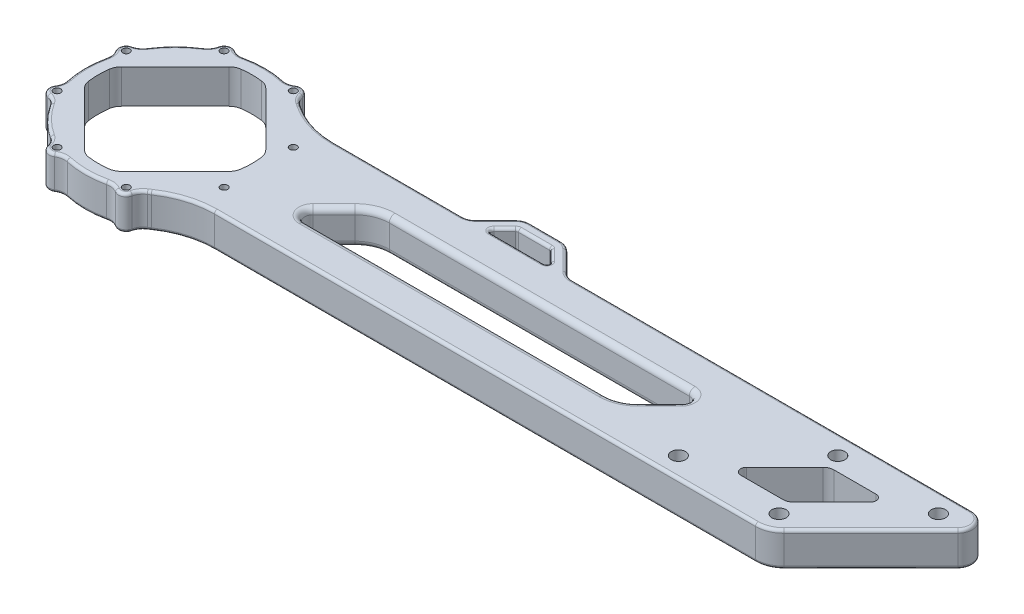
SolidWorks part; units mm, degrees
ref_plane "前视基准面" through (0, 0, 0) normal (0, 0, 1) x (1, 0, 0)
ref_plane "上视基准面" through (0, 0, 0) normal (0, 1, 0) x (1, 0, 0)
ref_plane "右视基准面" through (0, 0, 0) normal (1, 0, 0) x (0, 0, -1)
sketch "草图1" plane through (0, 0, 0) normal (0, 1, 0) x (1, 0, 0)
  line L0 (0, -31.8198) -> (31.8198, 0) construction
  line L9 (-29.3332, 12.1502) -> (-29.3332, -12.1502) construction
  line L10 (-29.3332, -12.1502) -> (-12.1502, -29.3332) construction
  line L11 (-12.1502, -29.3332) -> (12.1502, -29.3332) construction
  line L12 (12.1502, -29.3332) -> (29.3332, -12.1502) construction
  line L13 (29.3332, -12.1502) -> (29.3332, 12.1502) construction
  line L14 (29.3332, 12.1502) -> (12.1502, 29.3332) construction
  line L15 (12.1502, 29.3332) -> (-12.1502, 29.3332) construction
  line L16 (-12.1502, 29.3332) -> (-29.3332, 12.1502) construction
  line L17 (0, -31.8198) -> (-31.8198, 0) construction
  line L18 (31.8198, 0) -> (0, 31.8198) construction
  line L19 (-31.8198, 0) -> (0, 31.8198) construction
  line L20 (0, -31.8198) -> (0, 31.8198) construction
  line L21 (31.8198, 0) -> (-31.8198, 0) construction
  line L22 (-6.4825, -25.3373) -> (-25.3373, -6.4825)
  line L23 (-25.3373, 6.4825) -> (-6.4825, 25.3373)
  line L24 (6.4825, 25.3373) -> (25.3373, 6.4825)
  line L25 (25.3373, -6.4825) -> (6.4825, -25.3373)
  circle A0 centre (0, 0) radius 27 construction
  circle A1 centre (0, 0) radius 29.3332 construction
  arc A2 (-3.6168, -26.7567) -> (3.6168, -26.7567) centre (0, 0) ccw
  arc A3 (26.7567, -3.6168) -> (26.7567, 3.6168) centre (0, 0) ccw
  arc A4 (3.6168, 26.7567) -> (-3.6168, 26.7567) centre (0, 0) ccw
  arc A5 (-26.7567, -3.6168) -> (-26.7567, 3.6168) centre (0, 0) cw
  arc A6 (-3.6168, -26.7567) -> (-6.4825, -25.3373) centre (-2.947, -21.8017) cw
  arc A7 (3.6168, -26.7567) -> (6.4825, -25.3373) centre (2.947, -21.8017) ccw
  arc A8 (26.7567, -3.6168) -> (25.3373, -6.4825) centre (21.8017, -2.947) cw
  arc A9 (26.7567, 3.6168) -> (25.3373, 6.4825) centre (21.8017, 2.947) ccw
  arc A10 (3.6168, 26.7567) -> (6.4825, 25.3373) centre (2.947, 21.8017) cw
  arc A11 (-3.6168, 26.7567) -> (-6.4825, 25.3373) centre (-2.947, 21.8017) ccw
  arc A12 (-26.7567, 3.6168) -> (-25.3373, 6.4825) centre (-21.8017, 2.947) cw
  arc A13 (-26.7567, -3.6168) -> (-25.3373, -6.4825) centre (-21.8017, -2.947) ccw
  circle A14 centre (0, 0) radius 29 construction
  circle A15 centre (-12.1502, -29.3332) radius 2.75 construction
  circle A16 centre (0, 0) radius 31.75 construction
  circle A17 centre (-29.3332, -12.1502) radius 2.75 construction
  circle A18 centre (12.1502, -29.3332) radius 2.75 construction
  arc A19 (-14.8348, -29.9295) -> (-10.6736, -31.6531) centre (-12.1502, -29.3332) ccw
  arc A20 (10.6736, -31.6531) -> (14.6429, -28.1718) centre (12.1502, -29.3332) ccw construction
  arc A21 (-29.9295, -14.8348) -> (-30.2745, -9.5663) centre (-29.3332, -12.1502) cw construction
  arc A22 (-26.7942, -17.0334) -> (-17.0334, -26.7942) centre (0, 0) ccw
  arc A23 (-6.9019, -30.9907) -> (6.9019, -30.9907) centre (0, 0) ccw construction
  arc A24 (10.6736, -31.6531) -> (6.9019, -30.9907) centre (7.9888, -35.8712) ccw construction
  arc A25 (-10.6736, -31.6531) -> (-6.9019, -30.9907) centre (-7.9888, -35.8712) cw construction
  arc A26 (-14.8348, -29.9295) -> (-17.0334, -26.7942) centre (-19.7158, -31.0137) ccw
  arc A27 (-29.9295, -14.8348) -> (-26.7942, -17.0334) centre (-31.0137, -19.7158) cw
  circle A28 centre (-12.1502, -29.3332) radius 1.25
  circle A29 centre (-29.3332, -12.1502) radius 1.25
  arc A30 (-31.6531, -10.6736) -> (-29.9295, -14.8348) centre (-29.3332, -12.1502) ccw
  arc A31 (-31.6531, -10.6736) -> (-30.9907, -6.9019) centre (-35.8712, -7.9888) ccw
  arc A32 (-30.9907, 6.9019) -> (-30.9907, -6.9019) centre (0, 0) ccw
  arc A33 (-31.6531, 10.6736) -> (-30.9907, 6.9019) centre (-35.8712, 7.9888) cw
  circle A34 centre (-29.3332, 12.1502) radius 1.25
  arc A35 (-29.9295, 14.8348) -> (-31.6531, 10.6736) centre (-29.3332, 12.1502) ccw
  arc A36 (-29.9295, 14.8348) -> (-26.7942, 17.0334) centre (-31.0137, 19.7158) ccw
  arc A37 (-17.0334, 26.7942) -> (-26.7942, 17.0334) centre (0, 0) ccw
  arc A38 (-14.8348, 29.9295) -> (-17.0334, 26.7942) centre (-19.7158, 31.0137) cw
  circle A39 centre (-12.1502, 29.3332) radius 1.25
  arc A40 (-10.6736, 31.6531) -> (-14.8348, 29.9295) centre (-12.1502, 29.3332) ccw
  arc A41 (-10.6736, 31.6531) -> (-6.9019, 30.9907) centre (-7.9888, 35.8712) ccw
  arc A42 (6.9019, 30.9907) -> (-6.9019, 30.9907) centre (0, 0) ccw
  arc A43 (10.6736, 31.6531) -> (6.9019, 30.9907) centre (7.9888, 35.8712) cw
  circle A44 centre (12.1502, 29.3332) radius 1.25
  arc A45 (14.8348, 29.9295) -> (10.6736, 31.6531) centre (12.1502, 29.3332) ccw
  arc A46 (14.8348, 29.9295) -> (17.0334, 26.7942) centre (19.7158, 31.0137) ccw
  arc A47 (26.7942, 17.0334) -> (17.0334, 26.7942) centre (0, 0) ccw
  arc A48 (29.9295, 14.8348) -> (26.7942, 17.0334) centre (31.0137, 19.7158) cw
  circle A49 centre (29.3332, 12.1502) radius 1.25
  arc A50 (31.6531, 10.6736) -> (29.9295, 14.8348) centre (29.3332, 12.1502) ccw
  arc A51 (31.6531, 10.6736) -> (30.9907, 6.9019) centre (35.8712, 7.9888) ccw
  arc A52 (30.9907, -6.9019) -> (30.9907, 6.9019) centre (0, 0) ccw
  arc A53 (31.6531, -10.6736) -> (30.9907, -6.9019) centre (35.8712, -7.9888) cw
  circle A54 centre (29.3332, -12.1502) radius 1.25
  arc A55 (29.9295, -14.8348) -> (31.6531, -10.6736) centre (29.3332, -12.1502) ccw
  arc A56 (29.9295, -14.8348) -> (26.7942, -17.0334) centre (31.0137, -19.7158) ccw
  arc A57 (17.0334, -26.7942) -> (26.7942, -17.0334) centre (0, 0) ccw
  arc A58 (14.8348, -29.9295) -> (17.0334, -26.7942) centre (19.7158, -31.0137) cw
  circle A59 centre (12.1502, -29.3332) radius 1.25
  arc A60 (10.6736, -31.6531) -> (14.8348, -29.9295) centre (12.1502, -29.3332) ccw
  arc A61 (10.6736, -31.6531) -> (6.9019, -30.9907) centre (7.9888, -35.8712) ccw
  arc A62 (-6.9019, -30.9907) -> (6.9019, -30.9907) centre (0, 0) ccw
  arc A63 (-10.6736, -31.6531) -> (-6.9019, -30.9907) centre (-7.9888, -35.8712) cw
  point P13 (0, 0)
  point P32 (-5.3565, -26.4633)
  point P35 (5.3565, -26.4633)
  point P38 (26.4633, -5.3565)
  point P41 (26.4633, 5.3565)
  point P44 (5.3565, 26.4633)
  point P47 (-5.3565, 26.4633)
  point P50 (-26.4633, 5.3565)
  point P53 (-26.4633, -5.3565)
  point P72 (9.5663, -30.2745)
  point P75 (-9.5663, -30.2745)
  point P78 (-14.6429, -28.1718)
  point P81 (-28.1718, -14.6429)
  point P84 (-55.2795, -36.2672)
  point P155 (0, 0)
  dimension "D1" = 54
  dimension "D3" = 5
  dimension "D4" = 58
  dimension "D5" = 5.5
  dimension "D6" = 5
  dimension "D7" = 2.5
  dimension "D2" = 45
  dimension "D8" = 8
extrude "凸台-拉伸1" add sketch "草图1" along normal blind 12
sketch "草图2" plane through (0, 0, 0) normal (0, -1, 0) x (1, 0, 0)
  line L0 (0, 0) -> (250, 0) construction
  line L1 (23.8131, 21) -> (224.8579, 21)
  line L2 (23.8131, -21) -> (229, -21)
  line L3 (231.9289, 18.0711) -> (262.4645, -12.4645)
  line L4 (229, -21) -> (258.9289, -21)
  arc A0 (26.7942, 17.0334) -> (17.0334, 26.7942) centre (0, 0) ccw construction
  arc A1 (23.8131, 21) -> (23.8131, -21) centre (-10.231, 0) cw
  arc A2 (262.4645, -12.4645) -> (258.9289, -21) centre (258.9289, -16) cw
  arc A3 (224.8579, 21) -> (231.9289, 18.0711) centre (224.8579, 11) cw
  circle A4 centre (29.3332, 12.1502) radius 1.25
  circle A5 centre (29.3332, -12.1502) radius 1.25
  point P17 (229, 21)
  dimension "D4" = 5
  dimension "D5" = 10
  dimension "D6" = 40
  dimension "D1" = 250
  dimension "D2" = 42
  dimension "D3" = 45
extrude "凸台-拉伸2" add sketch "草图2" against normal up to surface (12 mm away) up to face at (0, 12, 0)
fillet "圆角1" radius 30 2 edges at (23.8131, 6, -21) (23.8131, 6, 21)
sketch "草图3" plane through (0, 0, 0) normal (0, -1, 0) x (1, 0, 0)
  line L0 (104.6336, -30.85) -> (93.7757, -30.85)
  line L1 (90.2402, -29.3855) -> (83.3191, -22.4645)
  line L2 (34.8147, -21) -> (258.9289, -21) construction
  line L3 (108.1691, -29.3855) -> (115.0902, -22.4645)
  line L4 (79.7836, -21) -> (76.2671, -21)
  line L5 (76.2671, -21) -> (76.2671, -10.4733)
  line L6 (76.2671, -10.4733) -> (121.997, -10.4733)
  line L7 (121.997, -10.4733) -> (121.997, -21)
  line L8 (121.997, -21) -> (118.6257, -21)
  line L9 (117.997, -17.022) -> (117.997, -17.022)
  line L13 (80.2671, -17.013) -> (80.2671, -17.013)
  line L14 (93.0686, -26.5571) -> (86.1476, -19.636) construction
  line L15 (104.6336, -26.85) -> (93.7757, -26.85)
  line L16 (105.3407, -26.5571) -> (112.2618, -19.636) construction
  line L17 (80.2671, -17.013) -> (80.2671, -14.4733) construction
  line L18 (80.2671, -14.4733) -> (117.997, -14.4733) construction
  line L19 (117.997, -14.4733) -> (117.997, -17.022) construction
  line L20 (108.4836, -21) -> (89.9257, -21)
  line L21 (105.3407, -26.5571) -> (109.1907, -22.7071)
  line L22 (93.0686, -26.5571) -> (89.2186, -22.7071)
  arc A0 (115.0902, -22.4645) -> (118.6257, -21) centre (118.6257, -26) cw
  arc A1 (83.3191, -22.4645) -> (79.7836, -21) centre (79.7836, -26) ccw
  arc A2 (93.7757, -30.85) -> (90.2402, -29.3855) centre (93.7757, -25.85) cw
  arc A3 (104.6336, -30.85) -> (108.1691, -29.3855) centre (104.6336, -25.85) ccw
  arc A6 (93.7757, -26.85) -> (93.0686, -26.5571) centre (93.7757, -25.85) cw
  arc A7 (104.6336, -26.85) -> (105.3407, -26.5571) centre (104.6336, -25.85) ccw
  arc A8 (86.1476, -19.636) -> (80.2671, -17.013) centre (79.7836, -26) ccw construction
  arc A9 (112.2618, -19.636) -> (117.997, -17.022) centre (118.6257, -26) cw construction
  arc A10 (89.9257, -21) -> (89.2186, -22.7071) centre (89.9257, -22) ccw
  arc A11 (108.4836, -21) -> (109.1907, -22.7071) centre (108.4836, -22) cw
  point P12 (116.5547, -21)
  point P15 (81.8547, -21)
  point P18 (91.7047, -30.85)
  point P21 (106.7047, -30.85)
  point P43 (87.5115, -21)
  point P46 (110.8978, -21)
  point P47 (93.0561, -26.5445)
  dimension "D4" = 5
  dimension "D6" = 1
  dimension "D1" = 9.85
  dimension "D2" = 15
  dimension "D3" = 45
  dimension "D5" = 4
extrude "凸台-拉伸3" add sketch "草图3" against normal up to surface (12 mm away) contours L0 A3 L3 A0 L8 L7 L6 L5 L4 A1 L1 A2 L20 A11 L21 A7 L15 A6 L22 A10 up to face at (26.3883, 12, 0.1603)
sketch "草图4" plane through (0, 12, 0) normal (0, 1, 0) x (1, 0, 0)
  line L0 (222.3726, -9) -> (207.6447, -9)
  line L1 (206.2304, -5.5858) -> (219.6447, 7.8284)
  line L2 (222.4731, 9) -> (237.201, 9)
  line L3 (238.6152, 5.5858) -> (225.201, -7.8284)
  arc A0 (225.201, -7.8284) -> (222.3726, -9) centre (222.3726, -5) cw
  arc A1 (207.6447, -9) -> (206.2304, -5.5858) centre (207.6447, -7) cw
  arc A2 (219.6447, 7.8284) -> (222.4731, 9) centre (222.4731, 5) cw
  arc A3 (238.6152, 5.5858) -> (237.201, 9) centre (237.201, 7) ccw
extrude "切除-拉伸1" cut sketch "草图4" against normal through all both and the other way through all
sketch "草图5" plane through (0, 0, 0) normal (0, -1, 0) x (1, 0, 0)
  circle A0 centre (254.1005, -14) radius 2.5
  circle A1 centre (218.7452, -14) radius 2.5
  circle A2 centre (226.1005, 14) radius 2.5
  circle A3 centre (190.7452, 14) radius 2.5
extrude "切除-拉伸2" cut sketch "草图5" against normal through all both and the other way through all
sketch "草图6" plane through (0, 0, 0) normal (0, -1, 0) x (1, 0, 0)
  line L0 (174.7282, -2.8787) -> (167.3643, 4.4853)
  line L1 (158.879, 8) -> (53.482, 8)
  line L2 (51.3607, 2.8787) -> (58.7247, -4.4853)
  line L3 (67.2099, -8) -> (172.6069, -8)
  line L4 (219.6447, -7.8284) -> (206.2304, 5.5858) construction
  line L5 (224.8579, 21) -> (34.8147, 21) construction
  line L7 (118.6257, -21) -> (258.9289, -21) construction
  arc A0 (58.7247, -4.4853) -> (67.2099, -8) centre (67.2099, 4) ccw
  arc A1 (167.3643, 4.4853) -> (158.879, 8) centre (158.879, -4) ccw
  arc A2 (53.482, 8) -> (51.3607, 2.8787) centre (53.482, 5) ccw
  arc A3 (174.7282, -2.8787) -> (172.6069, -8) centre (172.6069, -5) cw
  dimension "D3" = 12
  dimension "D4" = 3
  dimension "D1" = 13
  dimension "D2" = 13
extrude "切除-拉伸3" cut sketch "草图6" against normal through all
fillet "圆角2" radius 1 96 edges at (-30.9465, 12, -8.8537) (-31.75, 12, 0) (-30.9465, 12, 8.8537) (-31.8738, 12, 13.2026) (-28.143, 12, 15.622) (-22.4506, 12, 22.4506) (-15.622, 12, 28.143) (-13.2026, 12, 31.8738) (8.8537, 12, 30.9465) (13.2026, 12, 31.8738) (129.8363, 0, 21) (263.5483, 0, -17.9134) (247.1967, 0, 2.8033) (228.6847, 0, 20.2388) (228.6847, 12, 20.2388) (247.1967, 12, 2.8033) (263.5483, 12, -17.9134) (188.7773, 12, -21) (17.4694, 12, -26.512) (17.4694, 0, -26.512) (57.2991, 0, -21) (129.8363, 12, 21) (25.9637, 0, -22.3354) (25.9637, 12, -22.3354) (25.9637, 0, 22.3354) (25.9637, 12, 22.3354) (15.622, 12, 28.143) (99.2047, 0, -21) (188.7773, 0, -21) (99.2047, 12, -21) (57.2991, 12, -21) (89.0019, 12, -21.6173) (89.0019, 0, -21.6173) (105.0163, 12, -26.7739) (105.0163, 0, -26.7739) (107.2657, 12, -24.6321) (107.2657, 0, -24.6321) (99.2047, 12, -30.85) (99.2047, 0, -30.85) (91.8623, 12, -30.4694) (91.8623, 0, -30.4694) (86.7797, 12, -25.925) (86.7797, 0, -25.925) (81.697, 12, -21.3806) (81.697, 0, -21.3806) (116.7123, 0, -21.3806) (109.4075, 0, -21.6173) (99.2047, 0, -26.85) (93.3931, 0, -26.7739) (91.1436, 0, -24.6321) (106.547, 0, -30.4694) (111.6297, 0, -25.925) (116.7123, 12, -21.3806) (111.6297, 12, -25.925) (106.547, 12, -30.4694) (91.1436, 12, -24.6321) (93.3931, 12, -26.7739) (99.2047, 12, -26.85) (109.4075, 12, -21.6173) (17.4694, 12, 26.512) (-13.2026, 0, 31.8738) (-15.622, 0, 28.143) (-22.4506, 0, 22.4506) (-28.143, 0, 15.622) (-31.8738, 0, 13.2026) (-30.9465, 0, 8.8537) (-31.75, 0, 0) (-30.9465, 0, -8.8537) (-31.8738, 0, -13.2026) (-28.143, 0, -15.622) (-22.4506, 0, -22.4506) (-15.622, 0, -28.143) (-13.2026, 0, -31.8738) (-8.8537, 0, -30.9465) (0, 0, -31.75) (8.8537, 0, -30.9465) (13.2026, 0, -31.8738) (15.622, 0, -28.143) (17.4694, 0, 26.512) (15.622, 0, 28.143) (13.2026, 0, 31.8738) (8.8537, 0, 30.9465) (0, 0, 31.75) (-8.8537, 0, 30.9465) (-8.8537, 12, 30.9465) (15.622, 12, -28.143) (13.2026, 12, -31.8738) (8.8537, 12, -30.9465) (0, 12, -31.75) (-8.8537, 12, -30.9465) (-13.2026, 12, -31.8738) (-15.622, 12, -28.143) (-22.4506, 12, -22.4506) (0, 12, 31.75) (-28.143, 12, -15.622) (-31.8738, 12, -13.2026)
fillet "圆角3" radius 2 16 edges at (175.3786, 12, -6.1481) (119.9084, 12, -8) (62.6177, 12, -7.0866) (55.0427, 12, -0.8033) (50.7104, 12, 6.1481) (106.1805, 12, 8) (163.4712, 12, 7.0866) (175.3786, 0, -6.1481) (119.9084, 0, -8) (62.6177, 0, -7.0866) (55.0427, 0, -0.8033) (50.7104, 0, 6.1481) (106.1805, 0, 8) (163.4712, 0, 7.0866) (171.0463, 12, 0.8033) (171.0463, 0, 0.8033)
